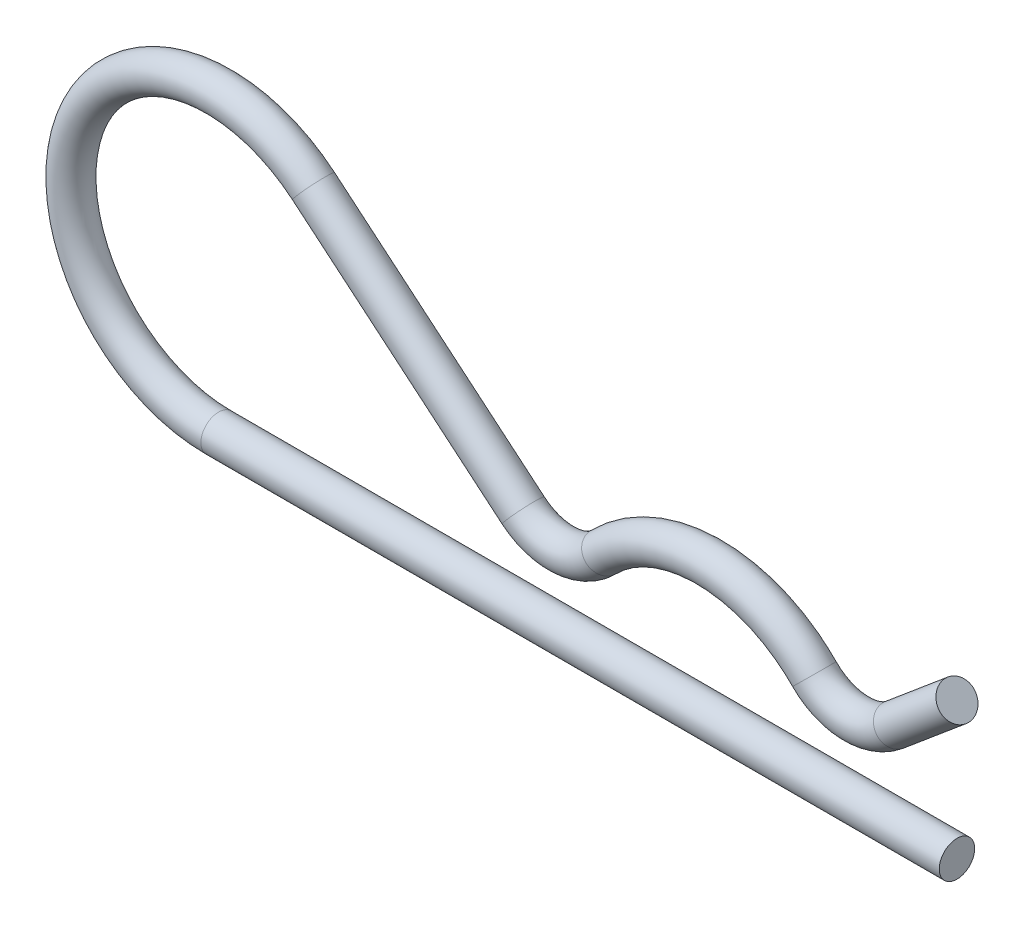
SolidWorks part; units mm, degrees
ref_plane "Front Plane" through (0, 0, 0) normal (0, 0, 1) x (1, 0, 0)
ref_plane "Top Plane" through (0, 0, 0) normal (0, 1, 0) x (1, 0, 0)
ref_plane "Right Plane" through (0, 0, 0) normal (1, 0, 0) x (0, 0, -1)
sketch "Sketch1" plane through (0, 0, 0) normal (0, 0, 1) x (1, 0, 0)
  line L0 (0, 0) -> (-63.5, 0)
  line L1 (-55.3366, 22.4288) -> (-37.3014, 7.2954)
  line L2 (-5.3706, 7.2954) -> (0, 11.8019)
  arc A0 (-63.5, 0) -> (-55.3366, 22.4288) centre (-63.5, 12.7) cw
  arc A1 (-37.3014, 7.2954) -> (-30.4074, 7.6317) centre (-34.036, 11.1869) ccw
  arc A2 (-30.4074, 7.6317) -> (-12.2646, 7.6317) centre (-21.336, -1.2565) cw
  arc A3 (-12.2646, 7.6317) -> (-5.3706, 7.2954) centre (-8.636, 11.1869) ccw
  point P12 (0, 0)
  point P14 (-8.636, 11.1869)
  point P15 (0, 0)
  point P16 (0, 0)
  dimension "D2" = 12.7
  dimension "D3" = 5.08
  dimension "D4" = 12.7
  dimension "D5" = 5.08
  dimension "D7" = 29.464
  dimension "D1" = 63.5
  dimension "D6" = 40
  dimension "D8" = 25.4
  dimension "D9" = 12.7
  dimension "D10" = 40
sketch "Sketch2" plane through (0, 0, 0) normal (1, 0, 0) x (0, 0, -1)
  circle A0 centre (0, 0) radius 1.524
  dimension "D1" = 3.048
sweep "Sweep1" add profiles "Sketch2" path "Sketch1"
